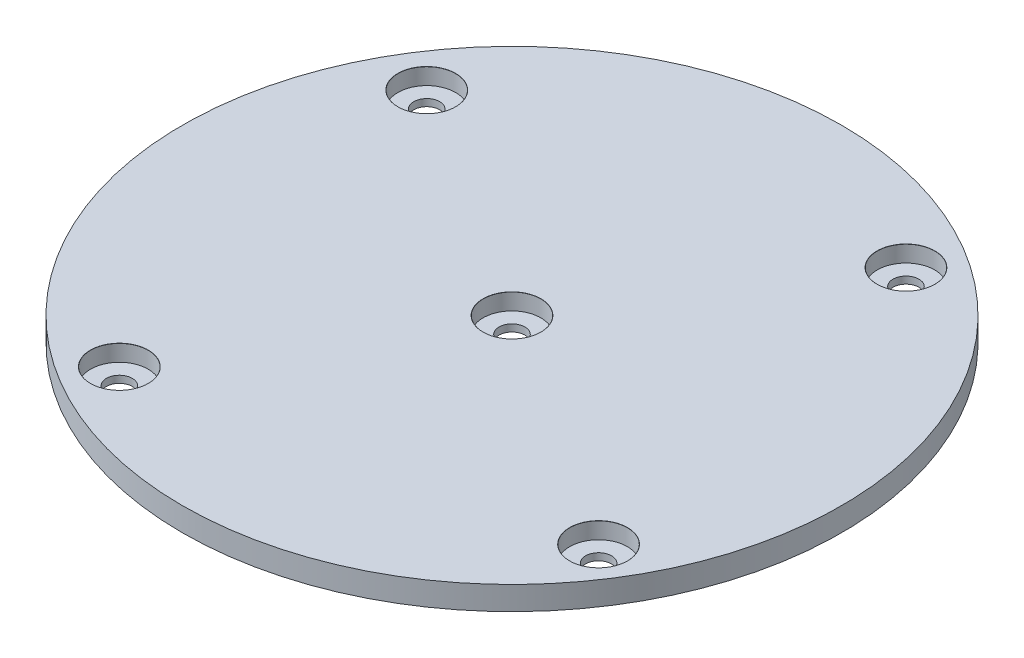
SolidWorks part; units mm, degrees
ref_plane "Front Plane" through (0, 0, 0) normal (0, 0, 1) x (1, 0, 0)
ref_plane "Top Plane" through (0, 0, 0) normal (0, 1, 0) x (1, 0, 0)
ref_plane "Right Plane" through (0, 0, 0) normal (1, 0, 0) x (0, 0, -1)
sketch "Sketch1" plane through (0, 0, 0) normal (0, 1, 0) x (1, 0, 0)
  circle A0 centre (0, 0) radius 70
  circle A1 centre (0, 0) radius 60 construction
  point P3 (0, 0)
  dimension "D1" = 140
  dimension "D2" = 120
extrude "Boss-Extrude1" add sketch "Sketch1" along normal blind 5 contours A0
sketch "Sketch4" plane through (0, 5, 0) normal (0, 1, 0) x (1, 0, 0)
  point P0 (-50.5027, 32.3956)
  dimension "D1" = 60
hole_wizard "CBORE for M5 Hex Head Bolt1" positions "Sketch4" profile "Sketch3" counterbore size "M5" standard "ISO" end condition through all
sketch "Sketch3" plane through (-50.5027, 5, -32.3956) normal (1, 0, 0) x (0, 0, 1)
  line L0 (0, 0) -> (0, 5)
  line L1 (0, 5) -> (2.75, 5)
  line L3 (2.75, 5) -> (2.75, 3.5)
  line L4 (6.119, 3.5) -> (2.75, 3.5)
  line L5 (6.119, 3.5) -> (6.119, 0.025)
  line L6 (6.119, 0.025) -> (6.144, 0)
  line L7 (6.144, 0) -> (0, 0)
  line L8 (-6.119, 0.025) -> (-6.144, 0) construction
  line L11 (0, -6.35) -> (0, 107.95) construction
  dimension "Thru Hole Dia." = 5.5
  dimension "Thru Hole Depth" = 5
  dimension "C'Bore Dia." = 12.238
  dimension "C'Bore Depth" = 3.5
  dimension "Near C'Sink Dia." = 12.288
  dimension "Near C'Sink Angle" = 90
pattern_circular "CirPattern1" count 4 over 360 about axis through (0.3921, 0, 0.2515) along (0, 1, 0) of "CBORE for M5 Hex Head Bolt1"
sketch "Sketch8" plane through (0, 5, 0) normal (0, 1, 0) x (1, 0, 0)
  point P0 (0, 0)
hole_wizard "CBORE for M5 Hex Head Bolt2" positions "Sketch8" profile "Sketch7" counterbore size "M5" standard "ISO" end condition through all
sketch "Sketch7" plane through (0, 5, 0) normal (1, 0, 0) x (0, 0, 1)
  line L0 (0, 0) -> (0, 5)
  line L1 (0, 5) -> (2.75, 5)
  line L3 (2.75, 5) -> (2.75, 3.5)
  line L4 (6.119, 3.5) -> (2.75, 3.5)
  line L5 (6.119, 3.5) -> (6.119, 0.025)
  line L6 (6.119, 0.025) -> (6.144, 0)
  line L7 (6.144, 0) -> (0, 0)
  line L8 (-6.119, 0.025) -> (-6.144, 0) construction
  line L11 (0, -6.35) -> (0, 107.95) construction
  dimension "Thru Hole Dia." = 5.5
  dimension "Thru Hole Depth" = 5
  dimension "C'Bore Dia." = 12.238
  dimension "C'Bore Depth" = 3.5
  dimension "Near C'Sink Dia." = 12.288
  dimension "Near C'Sink Angle" = 90
